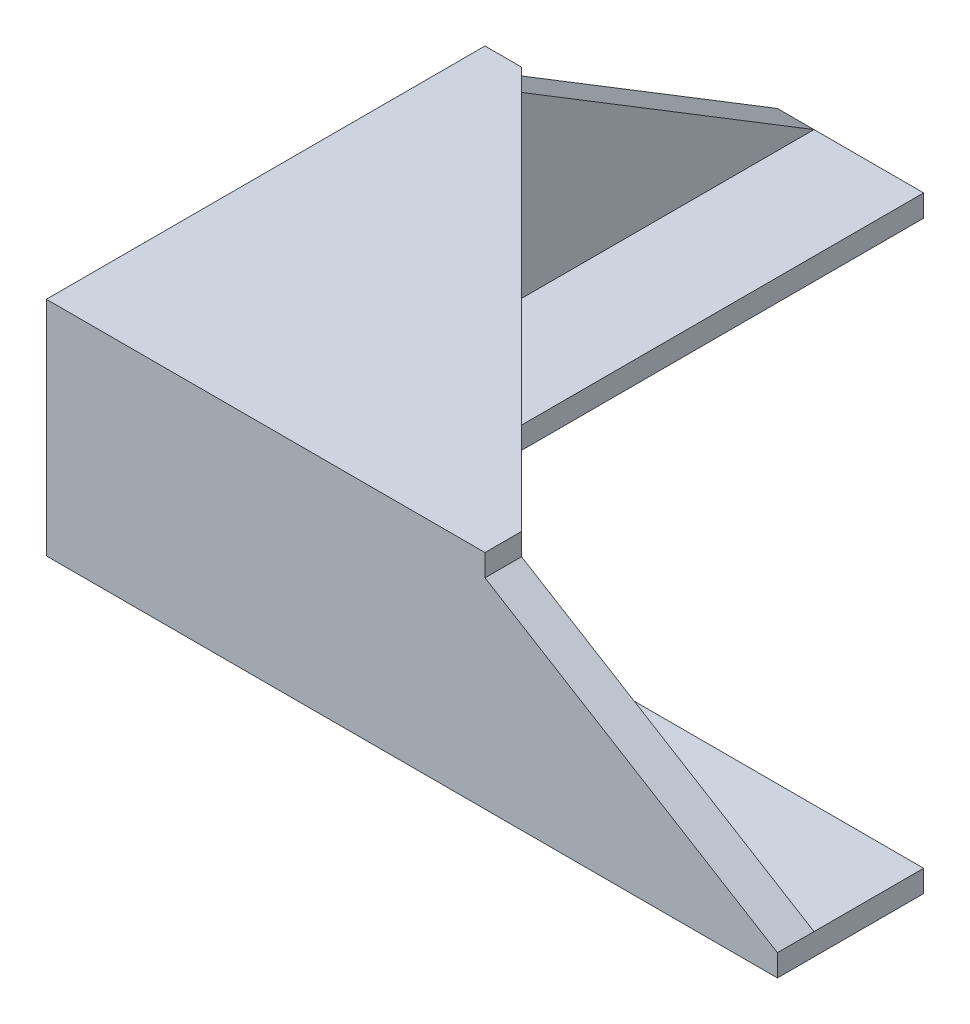
SolidWorks part; units mm, degrees
ref_plane "Front Plane" through (0, 0, 0) normal (0, 0, 1) x (1, 0, 0)
ref_plane "Top Plane" through (0, 0, 0) normal (0, 1, 0) x (1, 0, 0)
ref_plane "Right Plane" through (0, 0, 0) normal (1, 0, 0) x (0, 0, -1)
sketch "Sketch1" plane through (0, 0, 0) normal (0, 1, 0) x (1, 0, 0)
  line L0 (0, 0) -> (0, 100)
  line L1 (0, 100) -> (20, 100)
  line L2 (20, 100) -> (20, 20)
  line L3 (20, 20) -> (100, 20)
  line L4 (100, 20) -> (100, 0)
  line L5 (100, 0) -> (0, 0)
  dimension "D1" = 100
  dimension "D2" = 100
  dimension "D3" = 20
  dimension "D4" = 20
extrude "Boss-Extrude1" add sketch "Sketch1" along normal blind 3
sketch "Sketch2" plane through (0, 3, 0) normal (0, 1, 0) x (1, 0, 0)
  line L0 (0, 100) -> (0, 0)
  line L1 (0, 0) -> (100, 0)
  line L2 (100, 0) -> (100, 5)
  line L3 (100, 0) -> (100, 20) construction
  line L4 (100, 5) -> (5, 5)
  line L5 (5, 5) -> (5, 100)
  line L6 (20, 100) -> (0, 100) construction
  line L7 (5, 100) -> (0, 100)
  dimension "D1" = 5
  dimension "D2" = 5
extrude "Boss-Extrude2" add sketch "Sketch2" along normal blind 24.4
sketch "Sketch3" plane through (0, 27.4, 0) normal (0, 1, 0) x (1, 0, 0)
  line L0 (0, 0) -> (0, 60)
  line L1 (0, 100) -> (0, 0) construction
  line L2 (0, 60) -> (5, 60)
  line L3 (0, 0) -> (100, 0) construction
  line L4 (60, 0) -> (0, 0)
  line L5 (5, 5) -> (5, 100) construction
  line L6 (5, 60) -> (60, 5)
  line L7 (100, 5) -> (5, 5) construction
  line L8 (60, 5) -> (60, 0)
  dimension "D1" = 60
extrude "Boss-Extrude3" add sketch "Sketch3" along normal blind 3
sketch "Sketch4" plane through (0, 0, 0) normal (-1, 0, 0) x (0, 0, 1)
  line L0 (-60, 27.4) -> (-100, 3)
  line L1 (-100, 27.4) -> (-100, 0) construction
  line L2 (-100, 3) -> (-100, 27.4)
  line L3 (-100, 27.4) -> (-60, 27.4)
  line L4 (-100, 0) -> (0, 0) construction
  line L5 (-100, 27.4) -> (-60, 27.4) construction
  line L6 (-60, 30.4) -> (-60, 27.4) construction
  dimension "D1" = 3
extrude "Cut-Extrude2" cut sketch "Sketch4" against normal through all
sketch "Sketch5" plane through (0, 0, 0) normal (0, 0, 1) x (1, 0, 0)
  line L0 (60, 27.4) -> (100, 3)
  line L1 (100, 27.4) -> (100, 0) construction
  line L2 (100, 3) -> (100, 27.4)
  line L3 (100, 27.4) -> (60, 27.4)
  line L4 (0, 0) -> (100, 0) construction
  dimension "D1" = 3
extrude "Cut-Extrude3" cut sketch "Sketch5" against normal through all
